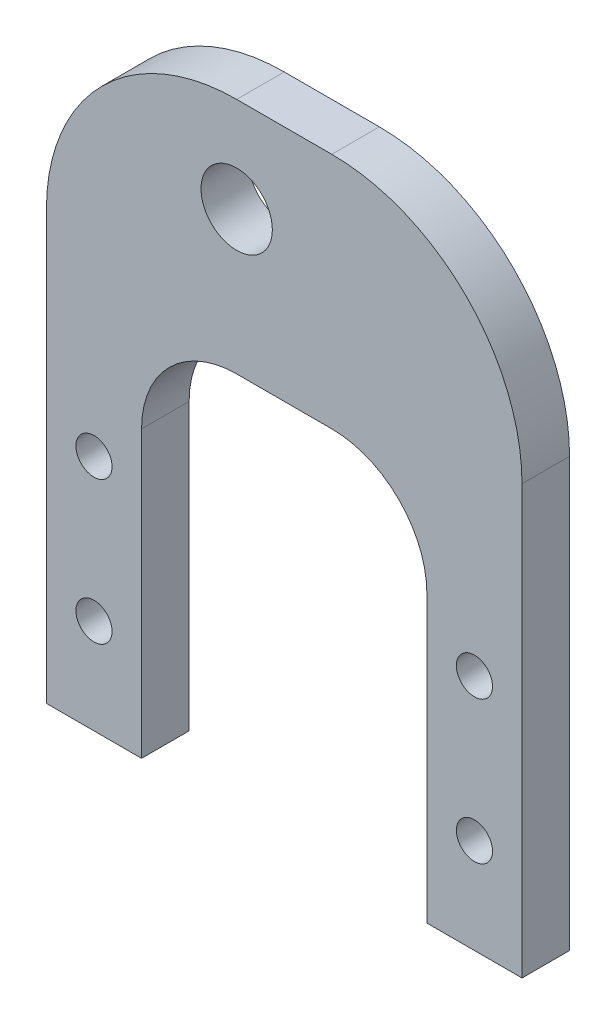
SolidWorks part; units mm, degrees
material "6061-T6 (SS)"
ref_plane "Front Plane" through (0, 0, 0) normal (0, 0, 1) x (1, 0, 0)
ref_plane "Top Plane" through (0, 0, 0) normal (0, 1, 0) x (1, 0, 0)
ref_plane "Right Plane" through (0, 0, 0) normal (1, 0, 0) x (0, 0, -1)
sketch "Sketch1" plane through (0, 0, 0) normal (0, 0, 1) x (1, 0, 0)
  line L1 (0, 0) -> (12.7, 0)
  line L2 (0, 0) -> (0, 82.55)
  line L5 (50.8, 0) -> (63.5, 0)
  line L8 (63.5, 0) -> (63.5, 82.55)
  line L11 (0, 82.55) -> (63.5, 82.55)
  line L13 (12.7, 0) -> (12.7, 50.8)
  line L14 (12.7, 50.8) -> (50.8, 50.8)
  line L15 (50.8, 50.8) -> (50.8, 0)
  dimension "D1" = 63.5
  dimension "D2" = 82.55
  dimension "D4" = 12.7
  dimension "D6" = 50.8
extrude "Boss-Extrude1" add sketch "Sketch1" along normal blind 6.35
sketch "Sketch2" plane through (0, 0, 6.35) normal (0, 0, 1) x (1, 0, 0)
  circle A0 centre (6.35, 12.7) radius 2.413
  circle A1 centre (6.35, 31.75) radius 2.413
  circle A2 centre (57.15, 12.7) radius 2.413
  circle A3 centre (57.15, 31.75) radius 2.413
  dimension "D1" = 4.826
  dimension "D2" = 4.826
  dimension "D3" = 6.35
  dimension "D4" = 12.7
  dimension "D5" = 19.05
  dimension "D6" = 50.8
extrude "Cut-Extrude1" cut sketch "Sketch2" against normal up to next
sketch "Sketch3" plane through (0, 0, 6.35) normal (0, 0, 1) x (1, 0, 0)
  circle A0 centre (25.4, 69.85) radius 4.7625
  dimension "D1" = 9.525
  dimension "D2" = 69.85
  dimension "D3" = 25.4
extrude "Cut-Extrude2" cut sketch "Sketch3" against normal up to next
ref_point "Point2"
fillet "Fillet1" radius 12.7 2 edges at (12.7, 50.8, 3.175) (50.8, 50.8, 3.175)
fillet "Fillet2" radius 25.4 2 edges at (63.5, 82.55, 3.175) (0, 82.55, 3.175)
